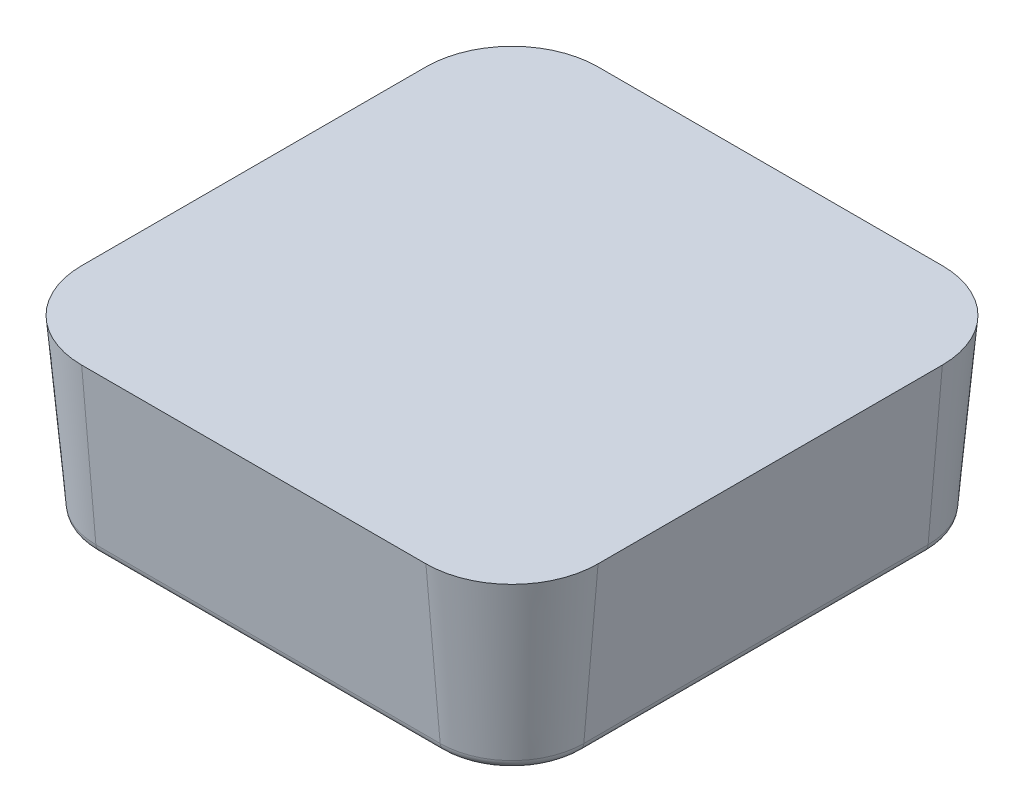
SolidWorks part; units mm, degrees
material "CA"
ref_plane "Front Plane" through (0, 0, 0) normal (0, 0, 1) x (1, 0, 0)
ref_plane "Top Plane" through (0, 0, 0) normal (0, 1, 0) x (1, 0, 0)
ref_plane "Right Plane" through (0, 0, 0) normal (1, 0, 0) x (0, 0, -1)
sketch "Sketch1" plane through (0, 0, 0) normal (0, 1, 0) x (1, 0, 0)
  line L1 (-6.35, -9.525) -> (6.35, -9.525)
  line L2 (-9.525, -6.35) -> (-9.525, 6.35)
  line L3 (-6.35, 9.525) -> (6.35, 9.525)
  line L4 (9.525, -6.35) -> (9.525, 6.35)
  line L5 (-9.525, -9.525) -> (9.525, 9.525) construction
  line L6 (-9.525, 9.525) -> (9.525, -9.525) construction
  arc A0 (-6.35, -9.525) -> (-9.525, -6.35) centre (-6.35, -6.35) cw
  arc A1 (6.35, -9.525) -> (9.525, -6.35) centre (6.35, -6.35) ccw
  arc A2 (6.35, 9.525) -> (9.525, 6.35) centre (6.35, 6.35) cw
  arc A3 (-9.525, 6.35) -> (-6.35, 9.525) centre (-6.35, 6.35) cw
  point P0 (0, 0)
  dimension "D3" = 3.175
  dimension "D1" = 19.05
  dimension "D2" = 19.05
extrude "Boss-Extrude1" add sketch "Sketch1" against normal blind 6.35 draft 5
sketch "Sketch12" plane through (0, 0, 0) normal (0, 0, 1) x (1, 0, 0)
  line L0 (0, 0) -> (0, -14.1739) construction
ref_plane "Plane2" through (0, 0, 0) normal (-0.2588, 0, 0.9659) x (0.9659, 0, 0.2588)
sketch "Sketch6" plane through (0, 0, 0) normal (-0.2588, 0, 0.9659) x (0.9659, 0, 0.2588)
  line L0 (0, 0) -> (0, -2.159) construction
  line L1 (0, -2.159) -> (-7.366, -9.525)
  line L2 (0, -2.159) -> (7.366, -9.525)
  line L3 (-7.366, -9.525) -> (7.366, -9.525)
  line L4 (-3.6684, 0) -> (8.5989, 0) construction
  dimension "D1" = 2.159
  dimension "D2" = 90
  dimension "D3" = 9.525
extrude "Cut-Extrude3" cut sketch "Sketch6" against normal through all
pattern_circular "CirPattern3" count 12 over 360 about axis through (0, 0, 0) along (0, 1, 0) of "Cut-Extrude3"
sketch "Sketch7" plane through (0, 0, 0) normal (0, 1, 0) x (1, 0, 0)
  line L4 (-6.35, -9.525) -> (6.35, -9.525)
  line L5 (9.525, -6.35) -> (9.525, 6.35)
  line L6 (6.35, 9.525) -> (-6.35, 9.525)
  line L7 (-9.525, 6.35) -> (-9.525, -6.35)
  line L8 (-6.35, -9.525) -> (6.35, -9.525)
  line L9 (9.525, -6.35) -> (9.525, 6.35)
  line L10 (6.35, 9.525) -> (-6.35, 9.525)
  line L11 (-9.525, 6.35) -> (-9.525, -6.35)
  line L20 (-6.35, -7.493) -> (6.35, -7.493)
  line L21 (7.493, -6.35) -> (7.493, 6.35)
  line L22 (6.35, 7.493) -> (-6.35, 7.493)
  line L23 (-7.493, 6.35) -> (-7.493, -6.35)
  line L24 (-6.35, -7.493) -> (6.35, -7.493)
  line L25 (7.493, -6.35) -> (7.493, 6.35)
  line L26 (6.35, 7.493) -> (-6.35, 7.493)
  line L27 (-7.493, 6.35) -> (-7.493, -6.35)
  arc A4 (-9.525, -6.35) -> (-6.35, -9.525) centre (-6.35, -6.35) ccw
  arc A5 (6.35, -9.525) -> (9.525, -6.35) centre (6.35, -6.35) ccw
  arc A6 (9.525, 6.35) -> (6.35, 9.525) centre (6.35, 6.35) ccw
  arc A7 (-6.35, 9.525) -> (-9.525, 6.35) centre (-6.35, 6.35) ccw
  arc A8 (-9.525, -6.35) -> (-6.35, -9.525) centre (-6.35, -6.35) ccw
  arc A9 (6.35, -9.525) -> (9.525, -6.35) centre (6.35, -6.35) ccw
  arc A10 (9.525, 6.35) -> (6.35, 9.525) centre (6.35, 6.35) ccw
  arc A11 (-6.35, 9.525) -> (-9.525, 6.35) centre (-6.35, 6.35) ccw
  arc A20 (-7.493, -6.35) -> (-6.35, -7.493) centre (-6.35, -6.35) ccw
  arc A21 (6.35, -7.493) -> (7.493, -6.35) centre (6.35, -6.35) ccw
  arc A22 (7.493, 6.35) -> (6.35, 7.493) centre (6.35, 6.35) ccw
  arc A23 (-6.35, 7.493) -> (-7.493, 6.35) centre (-6.35, 6.35) ccw
  arc A24 (-7.493, -6.35) -> (-6.35, -7.493) centre (-6.35, -6.35) ccw
  arc A25 (6.35, -7.493) -> (7.493, -6.35) centre (6.35, -6.35) ccw
  arc A26 (7.493, 6.35) -> (6.35, 7.493) centre (6.35, 6.35) ccw
  arc A27 (-6.35, 7.493) -> (-7.493, 6.35) centre (-6.35, 6.35) ccw
  dimension "D1" = 0
  dimension "D2" = 2.032
extrude "Boss-Extrude3" add sketch "Sketch7" against normal blind 6.35 draft 5
fillet "Fillet2" radius 0.381 16 edges at (-7.5511, -6.35, -7.5511) (0, -6.35, -8.0486) (7.5511, -6.35, -7.5511) (8.0486, -6.35, 0) (7.5511, -6.35, 7.5511) (0, -6.35, 8.0486) (-7.5511, -6.35, 7.5511) (-8.2022, -6.35, -8.2022) (0, -6.35, -8.9694) (8.2022, -6.35, -8.2022) (8.9694, -6.35, 0) (8.2022, -6.35, 8.2022) (0, -6.35, 8.9694) (-8.2022, -6.35, 8.2022) (-8.0486, -6.35, 0) (-8.9694, -6.35, 0)
ref_plane "Plane1" through (0, -5.969, 0) normal (0, -1, 0) x (-1, 0, 0)
sketch "Sketch8" plane through (0, -5.969, 0) normal (0, -1, 0) x (-1, 0, 0)
  line L0 (0, 0) -> (0, 13.8845) construction
  circle A0 centre (0, 7.493) radius 1.1811
  dimension "D1" = 2.3622
  dimension "D2" = 7.493
extrude "Boss-Extrude4" add sketch "Sketch8" against normal through all
sketch "Sketch9" plane through (0, -5.969, 0) normal (0, -1, 0) x (1, 0, 0)
  circle A0 centre (0, -7.493) radius 1.1811
extrude "Cut-Extrude4" cut sketch "Sketch9" along normal through all
sketch "Sketch10" plane through (0, 0, 0) normal (0, 0, 1) x (1, 0, 0)
  line L0 (0, 0) -> (0, 16.2069) construction
pattern_circular "CirPattern4" count 4 over 360 about axis through (0, 0, 0) along (0, 1, 0) of "Cut-Extrude4", "Boss-Extrude4"
sketch "Sketch11 - OFFSET .005" plane through (0, 0, 0) normal (0, 1, 0) x (1, 0, 0)
  line L8 (-6.35, -9.652) -> (6.35, -9.652)
  line L9 (9.652, -6.35) -> (9.652, 6.35)
  line L10 (6.35, 9.652) -> (-6.35, 9.652)
  line L11 (-9.652, 6.35) -> (-9.652, -6.35)
  line L12 (-6.35, -9.652) -> (6.35, -9.652) construction
  line L13 (9.652, -6.35) -> (9.652, 6.35) construction
  line L14 (6.35, 9.652) -> (-6.35, 9.652) construction
  line L15 (-9.652, 6.35) -> (-9.652, -6.35) construction
  arc A8 (-9.652, -6.35) -> (-6.35, -9.652) centre (-6.35, -6.35) ccw
  arc A9 (6.35, -9.652) -> (9.652, -6.35) centre (6.35, -6.35) ccw
  arc A10 (9.652, 6.35) -> (6.35, 9.652) centre (6.35, 6.35) ccw
  arc A11 (-6.35, 9.652) -> (-9.652, 6.35) centre (-6.35, 6.35) ccw
  arc A12 (-9.652, -6.35) -> (-6.35, -9.652) centre (-6.35, -6.35) ccw construction
  arc A13 (6.35, -9.652) -> (9.652, -6.35) centre (6.35, -6.35) ccw construction
  arc A14 (9.652, 6.35) -> (6.35, 9.652) centre (6.35, 6.35) ccw construction
  arc A15 (-6.35, 9.652) -> (-9.652, 6.35) centre (-6.35, 6.35) ccw construction
  dimension "D1" = 0.127
